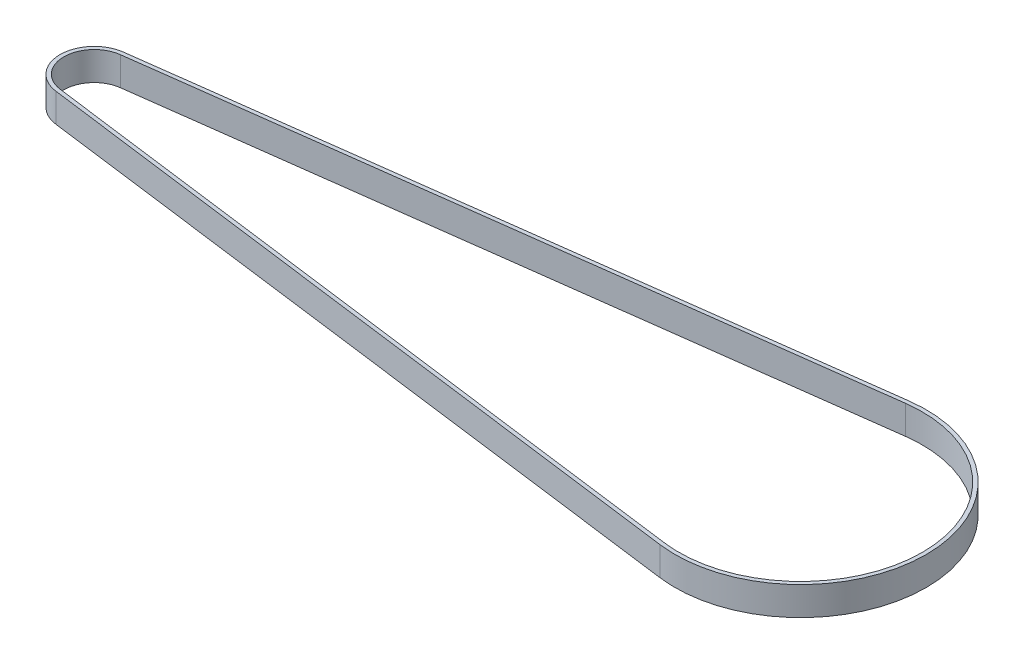
SolidWorks part; units mm, degrees
ref_plane "Front Plane" through (0, 0, 0) normal (0, 0, 1) x (1, 0, 0)
ref_plane "Top Plane" through (0, 0, 0) normal (0, 1, 0) x (1, 0, 0)
ref_plane "Right Plane" through (0, 0, 0) normal (1, 0, 0) x (0, 0, -1)
sketch "Sketch1" plane through (0, 0, 0) normal (0, 1, 0) x (1, 0, 0)
  line L0 (-148.8216, 6.2966) -> (-3.2995, 25.2856)
  line L1 (-148.8216, -6.2966) -> (-3.2995, -25.2856)
  line L2 (-148.9252, 7.0899) -> (-3.403, 26.0789)
  line L3 (-148.9252, -7.0899) -> (-3.403, -26.0789)
  arc A0 (-3.2995, -25.2856) -> (-3.2995, 25.2856) centre (0, 0) ccw
  arc A1 (-148.8216, 6.2966) -> (-148.8216, -6.2966) centre (-148, 0) ccw
  arc A2 (-3.403, -26.0789) -> (-3.403, 26.0789) centre (0, 0) ccw
  arc A3 (-148.9252, 7.0899) -> (-148.9252, -7.0899) centre (-148, 0) ccw
  dimension "D1" = 12.7
  dimension "D2" = 51
  dimension "D3" = 148
  dimension "D4" = 0.8
extrude "Boss-Extrude1" add sketch "Sketch1" along normal blind 6
